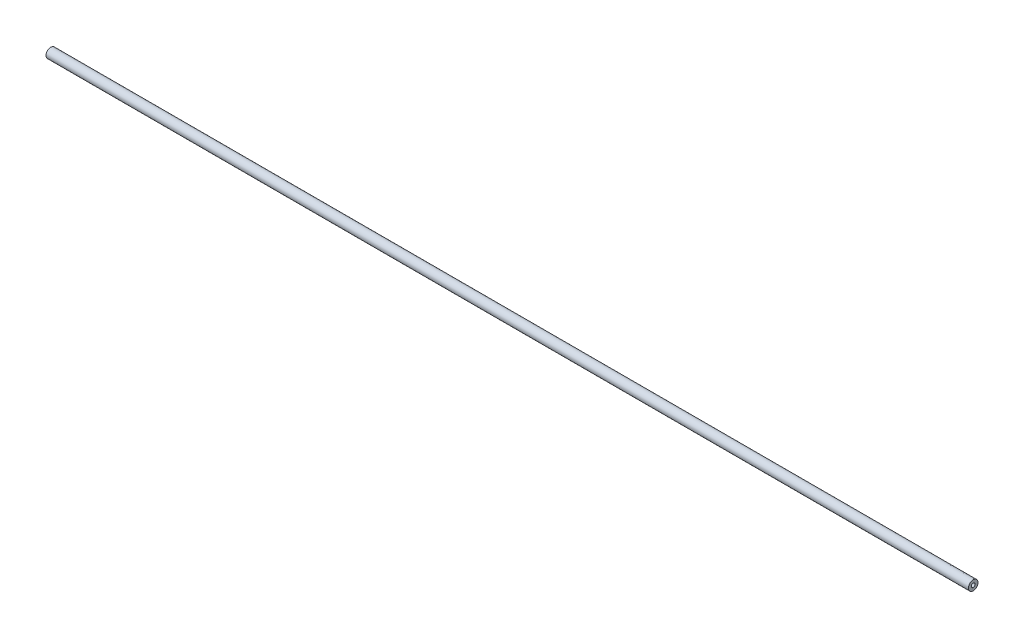
SolidWorks part; units mm, degrees
ref_plane "Ebene vorne" through (0, 0, 0) normal (0, 0, 1) x (1, 0, 0)
ref_plane "Ebene oben" through (0, 0, 0) normal (0, 1, 0) x (1, 0, 0)
ref_plane "Ebene rechts" through (0, 0, 0) normal (1, 0, 0) x (0, 0, -1)
sketch "Skizze1" plane through (0, 0, 0) normal (0, 0, 1) x (1, 0, 0)
  line L0 (-4.6381, 0) -> (3, 0) construction
  line L1 (3, 1.6) -> (0, 1.6)
  line L2 (3, 1.6) -> (3, 4)
  line L3 (3, 4) -> (-767, 4)
  line L4 (0, 1.6) -> (0, 0)
  line L5 (-767, 4) -> (-767, 0) construction
  line L6 (-382, 4) -> (-382, -63.8078) construction
  line L7 (-764, 1.6) -> (-764, 0)
  line L8 (-767, 1.6) -> (-764, 1.6)
  line L9 (-767, 1.6) -> (-767, 4)
  line L10 (0, 0) -> (-764, 0)
  dimension "D1" = 3
  dimension "D2" = 4
  dimension "D3" = 1.6
  dimension "D4" = 770
revolve "Rotation1" add sketch "Skizze1" angle 360 about L10
